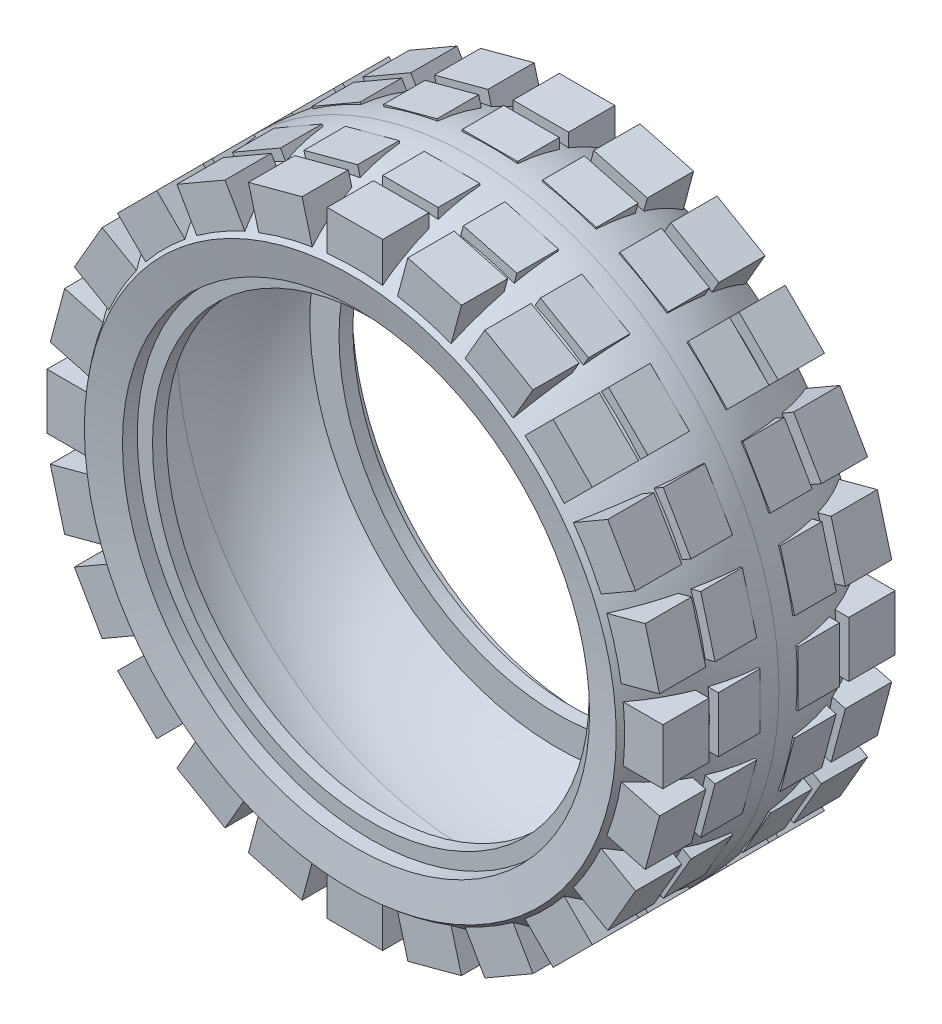
SolidWorks part; units mm, degrees
material "Rubber"
ref_plane "Front Plane" through (0, 0, 0) normal (0, 0, 1) x (1, 0, 0)
ref_plane "Top Plane" through (0, 0, 0) normal (0, 1, 0) x (1, 0, 0)
ref_plane "Right Plane" through (0, 0, 0) normal (1, 0, 0) x (0, 0, -1)
sketch "Sketch1" plane through (0, 0, 0) normal (1, 0, 0) x (0, 0, -1)
  line L0 (0, 0) -> (20, 0) construction
  line L1 (20, 0) -> (10, 0) construction
  line L2 (10, 0) -> (10, 255.3202) construction
  line L3 (-94.3772, 230) -> (-89.44, 202)
  line L4 (-89.44, 202) -> (-76.64, 202)
  line L5 (-76.64, 202) -> (-76.64, 188.8)
  line L6 (-76.64, 188.8) -> (-64.64, 188.8)
  line L7 (-64.64, 188.8) -> (-64.64, 214)
  line L8 (-64.64, 214) -> (-79.3708, 214)
  line L9 (-79.3708, 214) -> (-80.7814, 222)
  line L10 (99.3708, 214) -> (100.7814, 222)
  line L11 (84.64, 214) -> (99.3708, 214)
  line L12 (84.64, 188.8) -> (84.64, 214)
  line L13 (96.64, 188.8) -> (84.64, 188.8)
  line L14 (96.64, 202) -> (96.64, 188.8)
  line L15 (109.44, 202) -> (96.64, 202)
  line L16 (114.3772, 230) -> (109.44, 202)
  arc A0 (-94.3772, 230) -> (10, 266.3263) centre (7.1661, 106.3514) cw
  arc A1 (-80.7814, 222) -> (10, 254.3263) centre (4.3894, 126.4493) cw
  arc A2 (100.7814, 222) -> (10, 254.3263) centre (15.6106, 126.4493) ccw
  arc A3 (114.3772, 230) -> (10, 266.3263) centre (12.8339, 106.3514) ccw
  dimension "D13" = 128
  dimension "D14" = 160
  dimension "D1" = 86.64
  dimension "D2" = 202
  dimension "D3" = 188.8
  dimension "D4" = 12.8
  dimension "D5" = 12
  dimension "D6" = 28
  dimension "D7" = 8
  dimension "D8" = 12
  dimension "D9" = 100
  dimension "D10" = 12
  dimension "D11" = 12
  dimension "D12" = 266.3263
  dimension "D15" = 20
revolve "Revolve1" add sketch "Sketch1" angle 360 about L0
ref_plane "Plane1" through (0, 266.3263, 0) normal (0, -1, 0) x (-1, 0, 0)
sketch "Sketch2" plane through (0, 266.3263, 0) normal (0, -1, 0) x (-1, 0, 0)
  line L0 (-266.3263, 10) -> (266.3263, 10) construction
  line L1 (-266.3263, 10) -> (266.3263, 10) construction
  line L2 (0, 114.3772) -> (0, -94.3772) construction
  line L3 (-230, 114.3772) -> (230, 114.3772) construction
  line L4 (-230, -94.3772) -> (230, -94.3772) construction
  line L5 (24, 62.3772) -> (24, 26.3772)
  line L6 (-24, 110.3772) -> (24, 110.3772)
  line L7 (-24, 110.3772) -> (-24, 70.3772)
  line L8 (-24, 70.3772) -> (24, 70.3772)
  line L9 (24, 110.3772) -> (24, 70.3772)
  line L10 (-24, 110.3772) -> (24, 70.3772) construction
  line L11 (-24, 70.3772) -> (24, 110.3772) construction
  line L16 (24, 62.3772) -> (-24, 62.3772)
  line L17 (24, 26.3772) -> (-24, 26.3772)
  line L18 (-24, 62.3772) -> (-24, 26.3772)
  line L19 (-24, -50.3772) -> (24, -90.3772) construction
  line L20 (-24, -90.3772) -> (24, -50.3772) construction
  line L21 (-24, -42.3772) -> (-24, -6.3772)
  line L22 (24, -6.3772) -> (-24, -6.3772)
  line L23 (24, -90.3772) -> (24, -50.3772)
  line L24 (-24, -50.3772) -> (24, -50.3772)
  line L25 (-24, -90.3772) -> (-24, -50.3772)
  line L26 (-24, -90.3772) -> (24, -90.3772)
  line L27 (24, -42.3772) -> (24, -6.3772)
  line L28 (24, -42.3772) -> (-24, -42.3772)
  arc A0 (-230, 114.3772) -> (-266.3263, 10) centre (-106.3514, 12.8339) ccw construction
  point P14 (0, 90.3772)
  point P33 (0, -70.3772)
  dimension "D1" = 48
  dimension "D2" = 40
  dimension "D3" = 4
  dimension "D4" = 36
  dimension "D5" = 90
  dimension "D6" = 8
extrude "Boss-Extrude1" add sketch "Sketch2" along normal up to next
pattern_circular "CirPattern1" count 24 every 15 about axis through (0, 0, 0) along (0, 0, 1) of "Boss-Extrude1"
equation "\"scale\"= 8"
equation "\"D2@Sketch1\"=\"scale\" * 25.25mm"
equation "\"D3@Sketch1\"=\"scale\" * 23.60mm"
equation "\"D4@Sketch1\"=\"scale\" * 1.60mm"
equation "\"D5@Sketch1\"=\"scale\" * 1.50mm"
equation "\"D6@Sketch1\"=\"scale\" * 3.50mm"
equation "\"D7@Sketch1\"=\"scale\" * 1.00mm"
equation "\"D8@Sketch1\"=\"scale\" * 1.50mm"
equation "\"D10@Sketch1\"=\"scale\" * 1.50mm"
equation "\"D11@Sketch1\"=\"scale\" * 1.50mm"
equation "\"D12@Sketch1\"=\"scale\" * 33.29078835mm"
equation "\"D14@Sketch1\"=\"scale\" * 20.00mm"
equation "\"D13@Sketch1\"=\"scale\" * 16.00mm"
equation "\"D1@Sketch1\"=\"scale\" * 10.83mm"
equation "\"D1@Sketch2\"=\"scale\" * 6.00mm"
equation "\"D3@Sketch2\"=\"scale\" * 0.50mm"
equation "\"D2@Sketch2\"=\"scale\" * 5.00mm"
equation "\"D6@Sketch2\"=\"scale\" * 1.00mm"
equation "\"D4@Sketch2\"=\"scale\" * 4.50mm"
